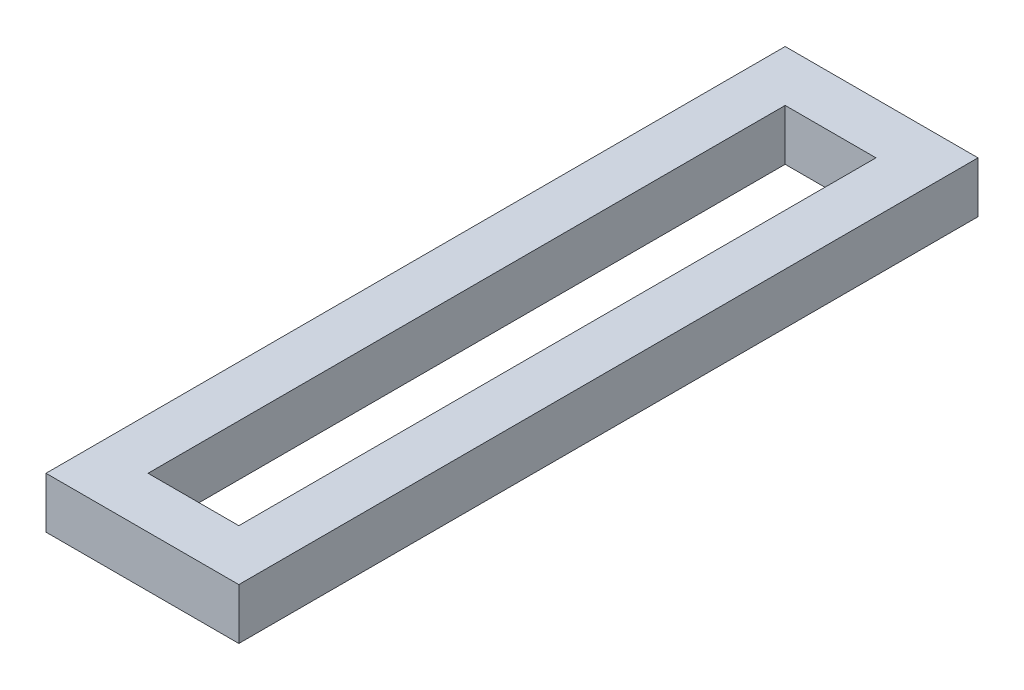
SolidWorks part; units mm, degrees
ref_plane "Front Plane" through (0, 0, 0) normal (0, 0, 1) x (1, 0, 0)
ref_plane "Top Plane" through (0, 0, 0) normal (0, 1, 0) x (1, 0, 0)
ref_plane "Right Plane" through (0, 0, 0) normal (1, 0, 0) x (0, 0, -1)
sketch "Sketch1" plane through (0, 0, 0) normal (0, 1, 0) x (1, 0, 0)
  line L0 (-14.125, 99.125) -> (14.125, 99.125)
  line L5 (-30, 115) -> (30, 115)
  line L6 (-30, 115) -> (-30, -115)
  line L7 (-30, -115) -> (30, -115)
  line L8 (30, 115) -> (30, -115)
  line L9 (14.125, 99.125) -> (14.125, -99.125)
  line L10 (-14.125, -99.125) -> (14.125, -99.125)
  line L11 (-14.125, 99.125) -> (-14.125, -99.125)
  point P4 (30, 0)
  point P5 (0, 115)
  dimension "D1" = 230
  dimension "D2" = 60
  dimension "D3" = 15.875
extrude "Boss-Extrude1" add sketch "Sketch1" along normal blind 15.875
